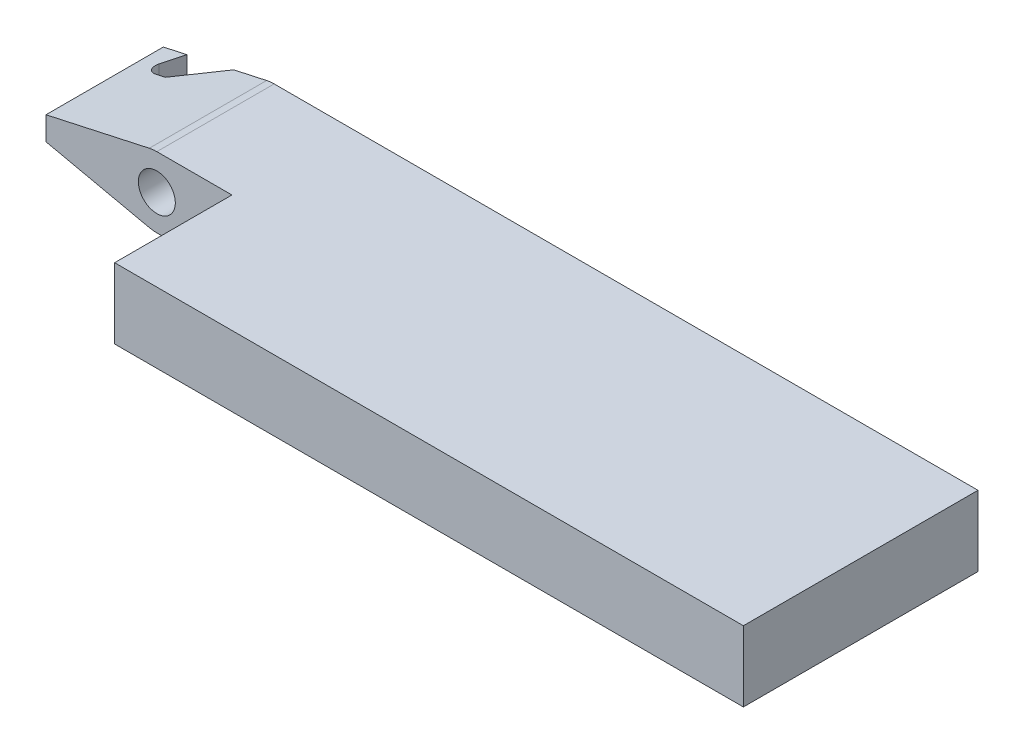
SolidWorks part; units mm, degrees
ref_plane "Front Plane" through (0, 0, 0) normal (0, 0, 1) x (1, 0, 0)
ref_plane "Top Plane" through (0, 0, 0) normal (0, 1, 0) x (1, 0, 0)
ref_plane "Right Plane" through (0, 0, 0) normal (1, 0, 0) x (0, 0, -1)
sketch "Sketch1" plane through (0, 0, 0) normal (0, 1, 0) x (1, 0, 0)
  line L1 (0, 0) -> (38.1, 0)
  line L2 (0, 0) -> (0, 12.7)
  line L3 (0, 12.7) -> (38.1, 12.7)
  line L4 (38.1, 0) -> (38.1, 12.7)
  dimension "D1" = 38.1
  dimension "D2" = 12.7
extrude "Boss-Extrude1" add sketch "Sketch1" along normal blind 3.81
sketch "Sketch2" plane through (0, 3.81, 0) normal (0, 1, 0) x (1, 0, 0)
  line L1 (0, 0) -> (4.064, 0)
  line L2 (0, 0) -> (0, 6.35)
  line L3 (0, 6.35) -> (4.064, 6.35)
  line L4 (4.064, 0) -> (4.064, 6.35)
  line L5 (0, 12.7) -> (0, 0) construction
  dimension "D1" = 4.064
extrude "Cut-Extrude1" cut sketch "Sketch2" against normal through all
sketch "Sketch4" plane through (0, 0, -12.7) normal (0, 0, -1) x (-1, 0, 0)
  line L0 (0, 3.81) -> (0, 0) construction
  circle A0 centre (0, 1.905) radius 1
  dimension "D1" = 2
extrude "Cut-Extrude2" cut sketch "Sketch4" against normal through all
sketch "Sketch5" plane through (0, 0, -12.7) normal (0, 0, -1) x (-1, 0, 0)
  line L0 (0.4079, 3.7658) -> (6, 2.54)
  line L1 (6, 2.54) -> (6, 1.27)
  line L2 (6, 1.27) -> (0.4079, 0.0442)
  line L3 (0, 1.905) -> (6, 1.905) construction
  circle A0 centre (0, 1.905) radius 1
  arc A1 (0.4079, 3.7658) -> (0.4079, 0.0442) centre (0, 1.905) ccw
  arc A2 (0, 2.905) -> (0, 0.905) centre (0, 1.905) ccw construction
  dimension "D1" = 6
  dimension "D2" = 1.27
extrude "Boss-Extrude2" add sketch "Sketch5" against normal up to surface (6.35 mm away) up to face at (1.5213, 1.905, -6.35)
sketch "Sketch6" plane through (0, 0, 0) normal (0, -1, 0) x (1, 0, 0)
  line L0 (-4.73, -12.7) -> (-5.3771, -10.922)
  line L1 (-0.4079, -12.7) -> (-6, -12.7) construction
  line L2 (-5.3771, -10.922) -> (-4.1071, -10.922)
  line L3 (-4.1071, -10.922) -> (-2.19, -12.7)
  line L4 (-2.19, -12.7) -> (-4.73, -12.7)
  dimension "D1" = 1.27
  dimension "D2" = 70
  dimension "D3" = 1.778
  dimension "D4" = 2.54
  dimension "D5" = 1.27
extrude "Cut-Extrude3" cut sketch "Sketch6" against normal through all
fillet "Fillet1" radius 0.508 1 edges at (-5.3771, 1.905, -10.922)
